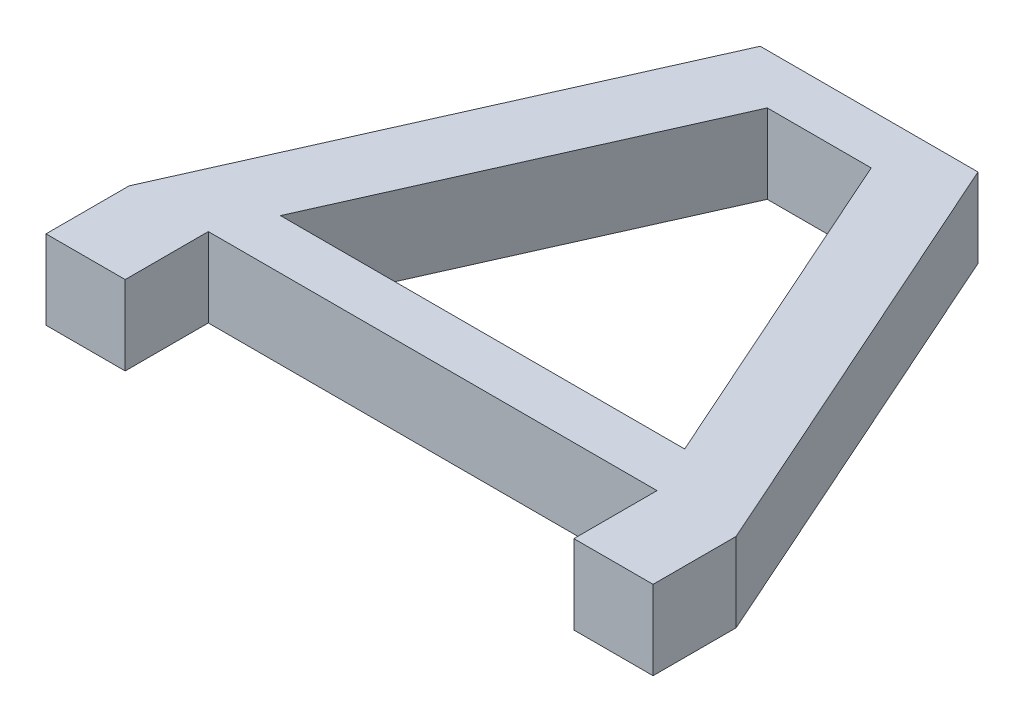
SolidWorks part; units mm, degrees
ref_plane "Front Plane" through (0, 0, 0) normal (0, 0, 1) x (1, 0, 0)
ref_plane "Top Plane" through (0, 0, 0) normal (0, 1, 0) x (1, 0, 0)
ref_plane "Right Plane" through (0, 0, 0) normal (1, 0, 0) x (0, 0, -1)
sketch "Sketch1" plane through (0, 0, 0) normal (0, 1, 0) x (1, 0, 0)
  line L0 (-63.5, 0) -> (63.5, 0) construction
  line L1 (0, 103) -> (0, 128.9207) construction
  line L2 (0, 0) -> (0, 103) construction
  line L3 (-12.5, 103) -> (12.5, 103)
  line L4 (-63.5, 0) -> (-63.5, -10) construction
  line L5 (-73.025, -10) -> (-53.975, -10)
  line L6 (-73.025, -10) -> (-73.025, 10)
  line L7 (-73.025, 10) -> (-26.1984, 115)
  line L8 (-26.1984, 115) -> (26.1984, 115)
  line L9 (-12.5, 103) -> (-48.6234, 22)
  line L10 (-53.975, 10) -> (-53.975, -10)
  line L11 (-53.975, 10) -> (53.975, 10)
  line L12 (48.6234, 22) -> (-48.6234, 22)
  line L13 (63.5, 0) -> (63.5, -10) construction
  line L14 (53.975, 10) -> (53.975, -10)
  line L15 (12.5, 103) -> (48.6234, 22)
  line L16 (73.025, 10) -> (26.1984, 115)
  line L17 (73.025, -10) -> (73.025, 10)
  line L18 (73.025, -10) -> (53.975, -10)
  point P8 (0, 103)
  point P9 (0, 0)
  point P15 (-63.5, -10)
  point P22 (0, 22)
  point P23 (0, 10)
  point P26 (0, 115)
  point P28 (63.5, -10)
  dimension "D1" = 103
  dimension "D3" = 12.5
  dimension "D4" = 19.05
  dimension "D5" = 127
  dimension "D6" = 10
  dimension "D7" = 10
  dimension "D8" = 12
  dimension "D2" = 12
  dimension "D9" = 20
extrude "Boss-Extrude1" add sketch "Sketch1" along normal blind 19.05
